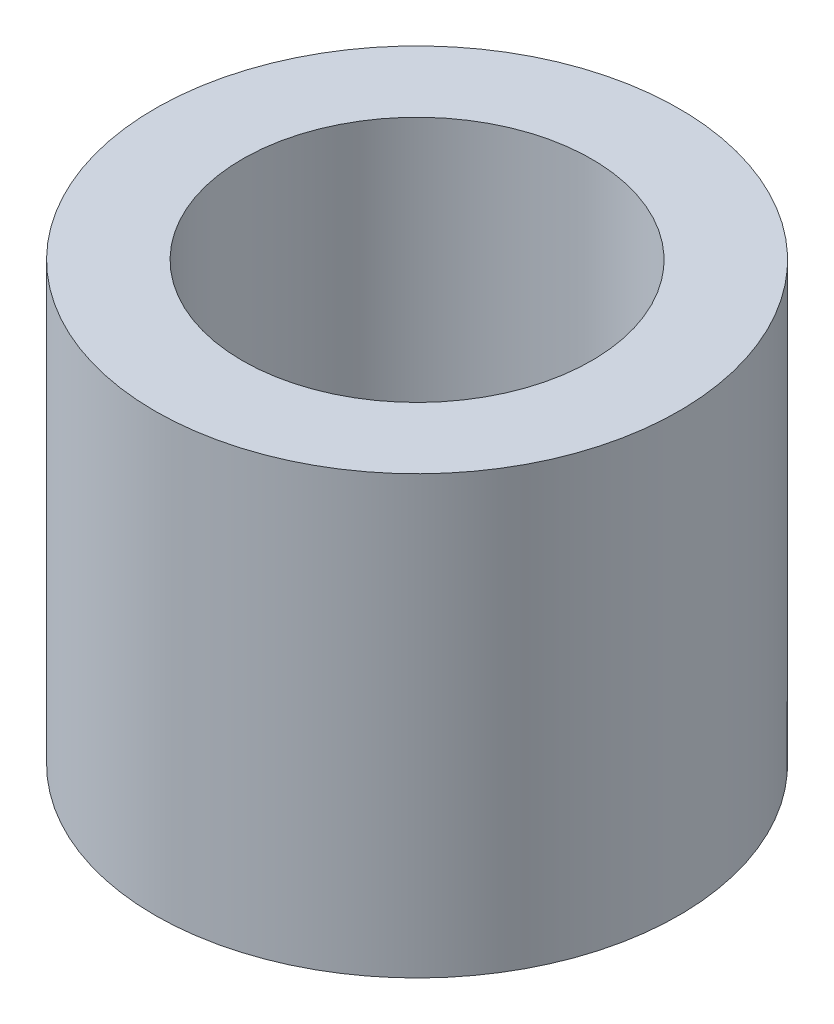
SolidWorks part; units mm, degrees
ref_plane "Front Plane" through (0, 0, 0) normal (0, 0, 1) x (1, 0, 0)
ref_plane "Top Plane" through (0, 0, 0) normal (0, 1, 0) x (1, 0, 0)
ref_plane "Right Plane" through (0, 0, 0) normal (1, 0, 0) x (0, 0, -1)
sketch "Sketch2" plane through (0, 0, 0) normal (0, 1, 0) x (1, 0, 0)
  circle A0 centre (0, 0) radius 2
  circle A1 centre (0, 0) radius 3
  dimension "D1" = 4
  dimension "D2" = 6
extrude "Boss-Extrude1" add sketch "Sketch2" along normal blind 5
